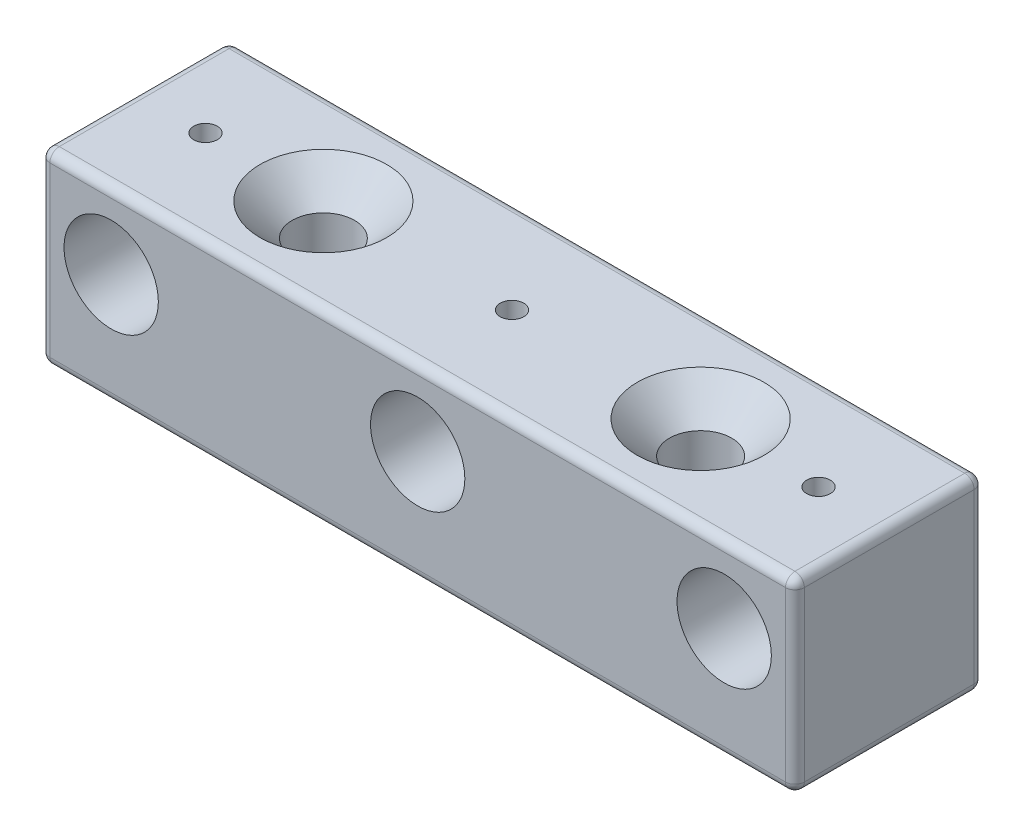
SolidWorks part; units mm, degrees
ref_plane "Front Plane" through (0, 0, 0) normal (0, 0, 1) x (1, 0, 0)
ref_plane "Top Plane" through (0, 0, 0) normal (0, 1, 0) x (1, 0, 0)
ref_plane "Right Plane" through (0, 0, 0) normal (1, 0, 0) x (0, 0, -1)
sketch "Sketch1" plane through (0, 0, 0) normal (0, 1, 0) x (1, 0, 0)
  line L1 (0, 0) -> (80, 0)
  line L2 (0, 0) -> (0, 20)
  line L3 (0, 20) -> (80, 20)
  line L4 (80, 0) -> (80, 20)
  line L5 (0, 0) -> (80, 20) construction
  line L6 (0, 20) -> (80, 0) construction
  point P4 (40, 10)
  dimension "D1" = 80
  dimension "D2" = 20
extrude "Boss-Extrude1" add sketch "Sketch1" along normal blind 19.85
sketch "Sketch2" plane through (0, 19.85, 0) normal (0, 1, 0) x (1, 0, 0)
  line L0 (0, 10) -> (80, 10) construction
  line L1 (0, 20) -> (0, 0) construction
  line L2 (80, 0) -> (80, 20) construction
  circle A0 centre (20, 10) radius 3.1
  circle A1 centre (60, 10) radius 3.1
  point P14 (40, 10)
  dimension "D2" = 6.2
  dimension "D1" = 40
  dimension "D3" = 20
extrude "Cut-Extrude1" cut sketch "Sketch2" against normal up to next
sketch "Sketch3" plane through (0, 0, 0) normal (0, 0, 1) x (1, 0, 0)
  line L0 (0, 19.85) -> (80, 19.85) construction
  line L1 (0, 19.85) -> (0, 0) construction
  line L2 (80, 19.85) -> (80, 0) construction
  line L3 (40, 0) -> (40, 19.85) construction
  line L4 (0, 0) -> (80, 0) construction
  circle A0 centre (7.5, 11.85) radius 5
  circle A1 centre (72.5, 11.85) radius 5
  circle A2 centre (40, 11.85) radius 5
  point P12 (40, 11.35)
  dimension "D1" = 10
  dimension "D2" = 7.5
  dimension "D3" = 7.5
  dimension "D4" = 8
extrude "Cut-Extrude2" cut sketch "Sketch3" against normal blind 15 contours A0 | A1 | A2
fillet "Fillet1" radius 1 12 edges at (0, 9.925, -20) (0, 9.925, 0) (80, 9.925, 0) (80, 9.925, -20) (40, 0, 0) (80, 0, -10) (40, 0, -20) (0, 0, -10) (40, 19.85, -20) (80, 19.85, -10) (40, 19.85, 0) (0, 19.85, -10)
hole_wizard "CSK for M6 SFHCS1" positions "3DSketch1" profile "Sketch4" countersink size "M6" standard "Autoliv NAM Metric"
sketch3d "3DSketch1"
  line L0 (60, 0, -10) -> (60, 19.85, -10) construction
  line L1 (20, 0, -10) -> (20, 19.85, -10) construction
  point P0 (18.9785, 0, -10.8427)
  point P2 (60, 19.85, -10)
  point P6 (20, 19.85, -10)
sketch "Sketch4" plane through (20, 19.85, -10) normal (1, 0, 0) x (0, 0, 1)
  line L0 (0, 0) -> (0, 19.85)
  line L1 (0, 19.85) -> (3.3, 19.85)
  line L2 (3.3, 19.85) -> (3.3, 3.42)
  line L3 (3.3, 3.42) -> (6.72, 0)
  line L5 (6.72, 0) -> (0, 0)
  line L6 (-3.3, 3.42) -> (-6.72, 0) construction
  line L11 (0, -6.35) -> (0, 107.95) construction
  dimension "Thru Hole Dia." = 6.6
  dimension "Thru Hole Depth" = 19.85
  dimension "Near C'Sink Dia." = 13.44
  dimension "Near C'Sink Angle" = 90
sketch "Sketch5" plane through (0, 19.85, 0) normal (0, 1, 0) x (1, 0, 0)
  line L0 (67.5, 0) -> (77.5, 0) construction
  line L1 (35, 0) -> (45, 0) construction
  line L2 (2.5, 0) -> (12.5, 0) construction
  line L3 (67.5, 0) -> (77.5, 0) construction
  line L4 (35, 0) -> (45, 0) construction
  line L5 (2.5, 0) -> (12.5, 0) construction
  line L6 (7.5, 0) -> (7.5, 19) construction
  line L7 (79, 19) -> (1, 19) construction
  line L8 (40, 0) -> (40, 19) construction
  line L9 (72.5, 0) -> (72.5, 19) construction
  line L10 (79, 10) -> (1, 10) construction
  line L11 (79, 1) -> (79, 19) construction
  line L12 (1, 19) -> (1, 1) construction
  point P20 (7.5, 10)
  point P21 (40, 10)
  point P22 (72.5, 10)
  point P23 (7.5, 10)
hole_wizard "M3x0.5 Tapped Hole1" positions "Sketch6" profile "Sketch7" tap size "M3x0.5" standard "Autoliv NAM Metric"
sketch "Sketch6" plane through (0, 19.85, 0) normal (0, 1, 0) x (1, 0, 0)
  point P0 (7.5, 10)
  point P3 (40, 10)
  point P6 (72.5, 10)
sketch "Sketch7" plane through (7.5, 19.85, -10) normal (1, 0, 0) x (0, 0, 1)
  line L0 (0, 0) -> (0, 3)
  line L1 (0, 3) -> (1.25, 3)
  line L2 (1.25, 3) -> (1.25, 0)
  line L5 (1.25, 0) -> (0, 0)
  line L11 (0, -6.35) -> (0, 107.95) construction
  dimension "Thru Tap Drill Dia." = 2.5
  dimension "Thru Tap Drill Depth" = 3
cosmetic thread "Hole Thread1" parameters "D2"=3
cosmetic thread "Hole Thread2" parameters "D2"=3
cosmetic thread "Hole Thread3" parameters "D2"=3
